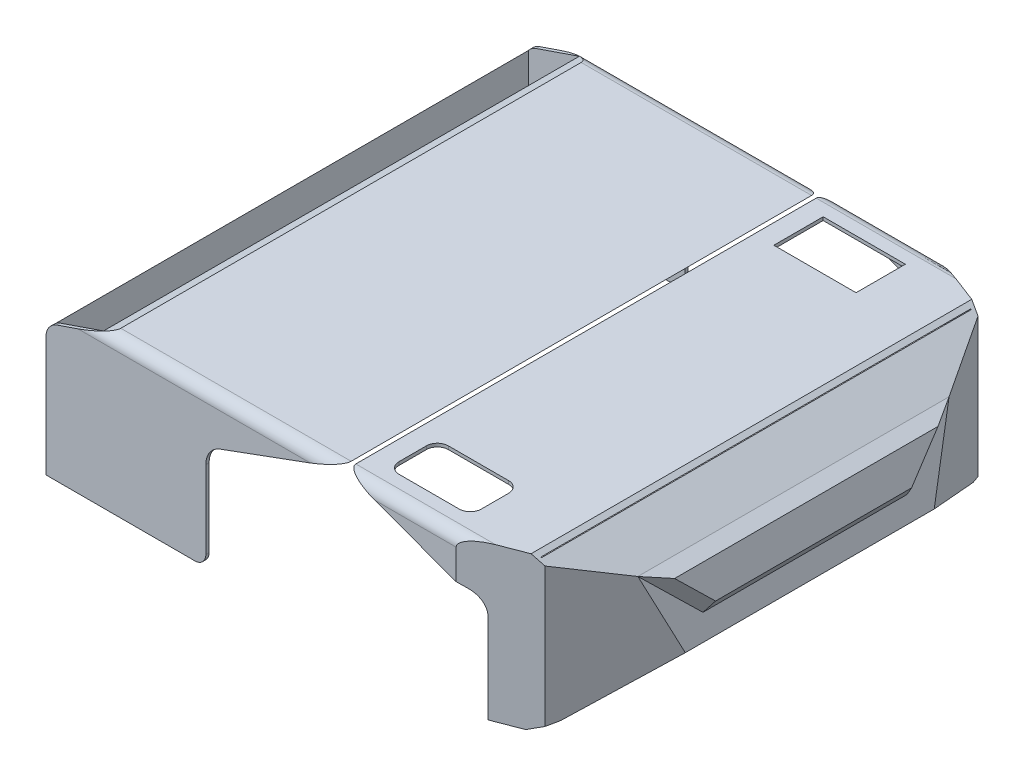
SolidWorks part; units mm, degrees
material "CA"
ref_plane "Front Plane" through (0, 0, 0) normal (0, 0, 1) x (1, 0, 0)
ref_plane "Top Plane" through (0, 0, 0) normal (0, 1, 0) x (1, 0, 0)
ref_plane "Right Plane" through (0, 0, 0) normal (1, 0, 0) x (0, 0, -1)
sketch "Sketch1" plane through (0, 0, 0) normal (0, 0, 1) x (1, 0, 0)
  line L1 (0, 0) -> (480, 0)
  line L2 (0, 0) -> (0, 140)
  line L3 (0, 140) -> (480, 140)
  line L4 (480, 0) -> (480, 140)
  dimension "D1" = 480
  dimension "D2" = 140
extrude "Boss-Extrude1" add sketch "Sketch1" along normal blind 440
sketch "Sketch2" plane through (0, 0, 440) normal (0, 0, 1) x (1, 0, 0)
  line L1 (0, 0) -> (420, 0)
  line L2 (0, 0) -> (0, 120)
  line L3 (0, 120) -> (420, 120)
  line L4 (420, 0) -> (420, 120)
  dimension "D1" = 120
  dimension "D2" = 420
sketch "Sketch3" plane through (0, 0, 440) normal (0, 0, 1) x (1, 0, 0)
  line L0 (0, 120) -> (58.2254, 140)
  line L1 (480, 140) -> (0, 140) construction
  line L2 (58.2254, 140) -> (423.4831, 140)
  line L3 (423.4831, 140) -> (461.8504, 111.6906)
  line L4 (461.8504, 111.6906) -> (480, 30.0603)
  line L5 (480, 0) -> (480, 140) construction
  line L6 (480, 30.0603) -> (420, 0)
  line L7 (0, 120) -> (0, 186.0028)
  line L8 (0, 186.0028) -> (591.5196, 186.0028)
  line L9 (591.5196, 186.0028) -> (591.5196, 0)
  line L10 (591.5196, 0) -> (420, 0)
  line L11 (480, 140) -> (0, 140) construction
extrude "Cut-Extrude2" cut sketch "Sketch3" against normal through all
chamfer "Chamfer1" distance 15 angle 60 1 edges at (480, 30.0603, 220)
sketch "Sketch4" plane through (0, 140, 0) normal (0, 1, 0) x (1, 0, 0)
  line L2 (476.7444, -333.5325) -> (476.7444, -106.4675)
  line L5 (374.147, -440) -> (432.7602, -417.4465)
  line L7 (432.7602, -417.4465) -> (476.7444, -333.5325)
  line L8 (476.7444, -333.5325) -> (476.7444, -220)
  line L9 (476.7444, -440) -> (476.7444, 0) construction
  line L10 (476.7444, -333.5325) -> (476.7444, -220)
  line L11 (476.7444, -220) -> (259.9754, -220) construction
  line L13 (374.147, -440) -> (571.4453, -440)
  line L14 (571.4453, -440) -> (571.4453, 0)
  line L15 (571.4453, 0) -> (374.147, 0)
  line L16 (374.147, 0) -> (432.7602, -22.5535)
  line L17 (432.7602, -22.5535) -> (476.7444, -106.4675)
  line L18 (423.4831, 0) -> (58.2254, 0) construction
  point P14 (476.7444, -220)
extrude "Cut-Extrude3" cut sketch "Sketch4" against normal blind 335 contours L2 L17 L16 L15 L14 L13 L5 L7
fillet "Fillet1" radius 10 2 edges at (216.1862, 140, 0) (216.1862, 140, 440)
fillet "Fillet2" radius 15 1 edges at (0, 120, 220)
sketch "Sketch6" plane through (463.7578, 103.1116, 0) normal (0.9762, 0.217, 0) x (0, 0, -1)
  line L0 (-361.9476, 8.7884) -> (-313.0975, -39.8352)
  line L1 (-313.0975, -39.8352) -> (-126.9025, -39.8352)
  line L2 (-361.9476, 8.7884) -> (-78.0524, 8.7884)
  line L3 (-333.5325, -59.8352) -> (-106.4675, -59.8352)
  line L4 (-220, -59.8352) -> (-220, -40.6647) construction
  line L5 (-78.0524, 8.7884) -> (-361.9476, 8.7884) construction
  line L6 (-78.0524, 8.7884) -> (-126.9025, -39.8352)
  point P10 (-220, -39.8352)
  point P15 (-220, 8.7884)
  line M9 (-78.0524, 8.7884) -> (-361.9476, 8.7884)
  dimension "D1" = 20
extrude "Boss-Extrude2" add sketch "Sketch6" along direction (-0.9762, -0.217, 0) on the side of the normal blind 10 draft 42 contours L4 L1 L6 M9 | L1 L4 L2 L0
sketch "Sketch7" plane through (0, 0, 0) normal (0, -1, 0) x (1, 0, 0)
  line L1 (428.0503, 416.0444) -> (373.5897, 437)
  line L2 (373.5897, 437) -> (3, 437)
  line L3 (3, 437) -> (3, 3)
  line L4 (3, 3) -> (373.5897, 3)
  line L5 (373.5897, 3) -> (428.0503, 23.9556)
  line L14 (428.0503, 23.9556) -> (428.0503, 416.0444)
extrude "Cut-Extrude4" cut sketch "Sketch7" against normal offset from surface (137 mm away) 3 contours L1 L2 L3 L4 L5 L14 up to face at (293.948, 140, 220)
sketch "Sketch8" plane through (0, 140, 0) normal (0, 1, 0) x (1, 0, 0)
  line L0 (58.2254, -220) -> (508.1789, -220) construction
  line L1 (58.2254, -10) -> (58.2254, -430) construction
  line L2 (328, -61.5371) -> (328, -26.5371) construction
  line L3 (200.5, -44.0371) -> (375.5, -44.0371) construction
  line L5 (375.5, -39.5371) -> (375.5, -48.5371) construction
  line L6 (300.5, -373.4629) -> (355.5, -373.4629)
  line L7 (290.5, -66.5371) -> (365.5, -66.5371)
  line L8 (290.5, -66.5371) -> (290.5, -21.5371)
  line L9 (290.5, -21.5371) -> (365.5, -21.5371)
  line L10 (365.5, -66.5371) -> (365.5, -21.5371)
  line L11 (290.5, -66.5371) -> (365.5, -21.5371) construction
  line L12 (290.5, -21.5371) -> (365.5, -66.5371) construction
  line L13 (290.5, -383.4629) -> (290.5, -408.4629)
  line L14 (300.5, -418.4629) -> (355.5, -418.4629)
  line L15 (365.5, -383.4629) -> (365.5, -408.4629)
  arc A0 (300.5, -373.4629) -> (290.5, -383.4629) centre (300.5, -383.4629) ccw
  arc A1 (355.5, -373.4629) -> (365.5, -383.4629) centre (355.5, -383.4629) cw
  arc A2 (290.5, -408.4629) -> (300.5, -418.4629) centre (300.5, -408.4629) ccw
  arc A3 (355.5, -418.4629) -> (365.5, -408.4629) centre (355.5, -408.4629) ccw
  point P17 (328, -44.0371)
  point P25 (290.5, -373.4629)
  point P28 (365.5, -373.4629)
  point P31 (290.5, -418.4629)
  point P34 (365.5, -418.4629)
  dimension "D3" = 10
  dimension "D1" = 75
  dimension "D2" = 45
extrude "Cut-Extrude5" cut sketch "Sketch8" against normal blind 10
sketch "Sketch9" plane through (0, 0, 440) normal (0, 0, 1) x (1, 0, 0)
  line L0 (270.5, 48.5752) -> (270.5, 127) construction
  line L1 (270.5, 140.7751) -> (158.9171, 99.8501)
  line L2 (145.8038, 81.0732) -> (145.8038, 0)
  line L3 (0, 0) -> (374.147, 0) construction
  line L4 (145.8038, 0) -> (395.1962, 0)
  line L5 (395.1962, 81.0732) -> (395.1962, 0)
  line L6 (270.5, 140.7751) -> (382.0829, 99.8501)
  arc A1 (158.9171, 99.8501) -> (145.8038, 81.0732) centre (165.8038, 81.0732) ccw
  arc A2 (382.0829, 99.8501) -> (395.1962, 81.0732) centre (375.1962, 81.0732) cw
  point P15 (270.5, 0)
  dimension "D1" = 20
extrude "Cut-Extrude6" cut sketch "Sketch9" against normal blind 674
sketch "Sketch10" plane through (0, 0, 440) normal (0, 0, 1) x (1, 0, 0)
  line L0 (360.1962, 33.9966) -> (319.6001, 53.8513)
  line L1 (395.1962, 0) -> (395.1962, 81.0732) construction
  line L2 (325.2066, 44.8682) -> (325.2066, 0)
  line L3 (0, 0) -> (145.8038, 0) construction
  line L4 (325.2066, 0) -> (360.1962, 0)
  line L5 (360.1962, 0) -> (360.1962, 33.9966)
  arc A0 (319.6001, 53.8513) -> (325.2066, 44.8682) centre (315.2066, 44.8682) cw
  dimension "D1" = 10
extrude "Cut-Extrude7" cut sketch "Sketch10" against normal through all
fillet "Fillet3" radius 10 2 edges at (145.8038, 0, 1.5) (145.8038, 0, 438.5)
